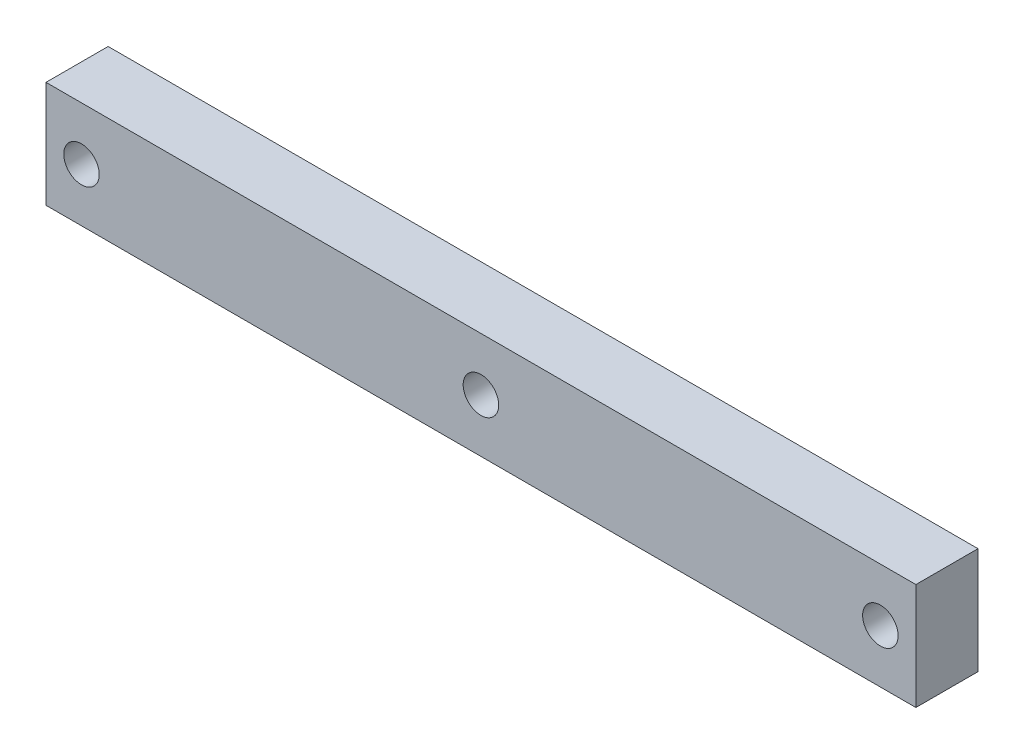
SolidWorks part; units mm, degrees
ref_plane "Front Plane" through (0, 0, 0) normal (0, 0, 1) x (1, 0, 0)
ref_plane "Top Plane" through (0, 0, 0) normal (0, 1, 0) x (1, 0, 0)
ref_plane "Right Plane" through (0, 0, 0) normal (1, 0, 0) x (0, 0, -1)
sketch "Sketch1" plane through (0, 0, 0) normal (0, 0, 1) x (1, 0, 0)
  line L0 (0, 6) -> (0, -6) construction
  line L1 (-49, -6) -> (49, -6)
  line L2 (-49, -6) -> (-49, 6)
  line L3 (-49, 6) -> (49, 6)
  line L4 (49, -6) -> (49, 6)
  line L5 (-49, -6) -> (49, 6) construction
  line L6 (-49, 6) -> (49, -6) construction
  circle A0 centre (0, 0) radius 2
  circle A1 centre (45, 0) radius 2
  circle A2 centre (-45, 0) radius 2
  point P0 (0, 0)
  dimension "D3" = 4
  dimension "D5" = 45
  dimension "D1" = 12
  dimension "D2" = 98
  dimension "D4" = 2
extrude "Boss-Extrude1" add sketch "Sketch1" along normal blind 7
